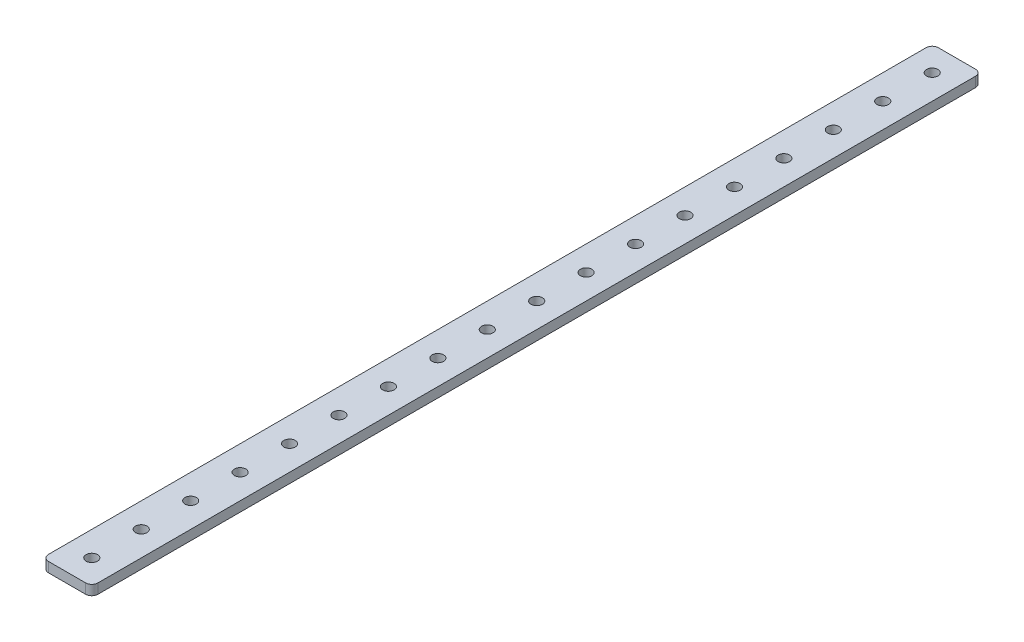
SolidWorks part; units mm, degrees
ref_plane "Front Plane" through (0, 0, 0) normal (0, 0, 1) x (1, 0, 0)
ref_plane "Top Plane" through (0, 0, 0) normal (0, 1, 0) x (1, 0, 0)
ref_plane "Right Plane" through (0, 0, 0) normal (1, 0, 0) x (0, 0, -1)
ref_plane "Plane1" through (0, 3.2, 0) normal (0, 1, 0) x (1, 0, 0)
sketch "Sketch1" plane through (0, 3.2, 0) normal (0, 1, 0) x (1, 0, 0)
  line L0 (8, 2) -> (8, 286)
  line L1 (6, 288) -> (-6, 288)
  line L2 (-8, 286) -> (-8, 2)
  line L3 (-6, 0) -> (6, 0)
  circle A0 centre (0, 280) radius 1.85
  circle A1 centre (0, 264) radius 1.85
  circle A2 centre (0, 248) radius 1.85
  circle A3 centre (0, 232) radius 1.85
  circle A4 centre (0, 216) radius 1.85
  circle A5 centre (0, 200) radius 1.85
  circle A6 centre (0, 184) radius 1.85
  circle A7 centre (0, 168) radius 1.85
  circle A8 centre (0, 152) radius 1.85
  circle A9 centre (0, 136) radius 1.85
  circle A10 centre (0, 120) radius 1.85
  circle A11 centre (0, 104) radius 1.85
  circle A12 centre (0, 88) radius 1.85
  circle A13 centre (0, 72) radius 1.85
  circle A14 centre (0, 56) radius 1.85
  circle A15 centre (0, 40) radius 1.85
  circle A16 centre (0, 24) radius 1.85
  circle A17 centre (0, 8) radius 1.85
  arc A18 (8, 286) -> (6, 288) centre (6, 286) ccw
  arc A19 (-6, 288) -> (-8, 286) centre (-6, 286) ccw
  arc A20 (-8, 2) -> (-6, 0) centre (-6, 2) ccw
  arc A21 (6, 0) -> (8, 2) centre (6, 2) ccw
extrude "Boss-Extrude1" add sketch "Sketch1" against normal blind 3.2
